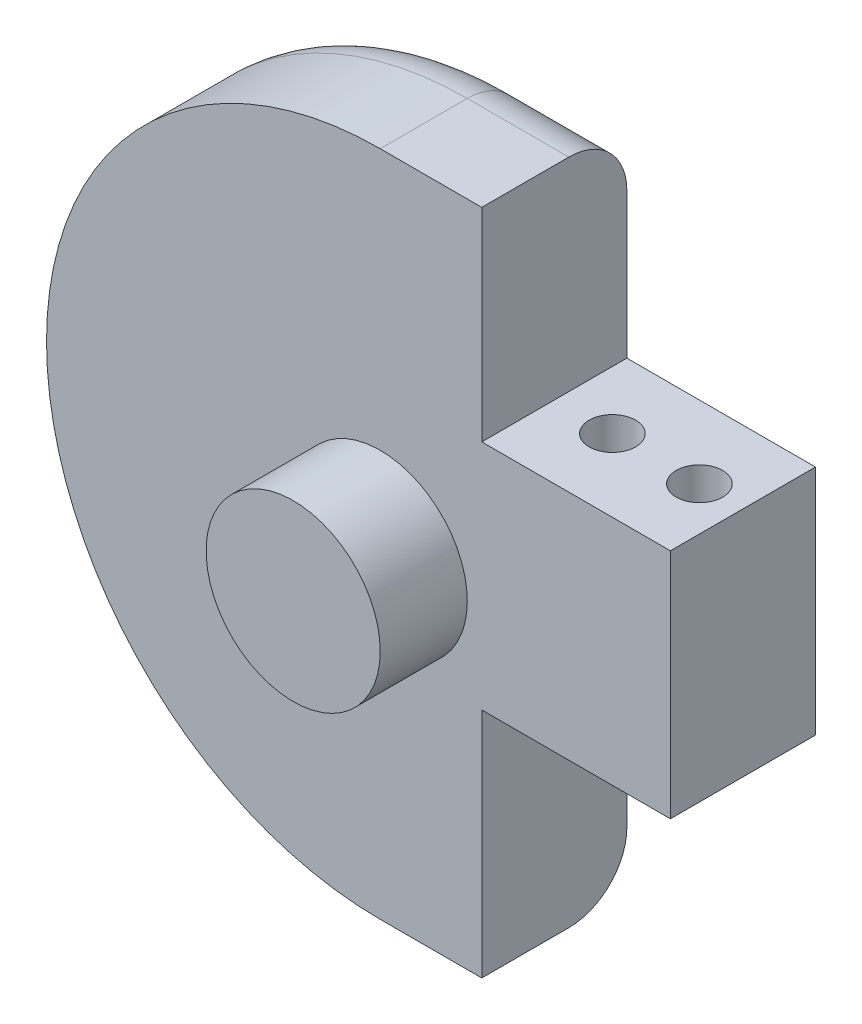
SolidWorks part; units mm, degrees
ref_plane "Front" through (0, 0, 0) normal (0, 0, 1) x (1, 0, 0)
ref_plane "Top" through (0, 0, 0) normal (0, 1, 0) x (1, 0, 0)
ref_plane "Right" through (0, 0, 0) normal (1, 0, 0) x (0, 0, -1)
sketch "Sketch1" plane through (0, 0, 0) normal (0, 0, 1) x (1, 0, 0)
  line L0 (-11, 0) -> (-1, 0) construction
  line L1 (-1, 0) -> (9, 0) construction
  line L2 (3.5, 12) -> (3.5, 5)
  line L3 (3.5, 5) -> (10, 5)
  line L4 (10, -3) -> (3.5, -3)
  line L5 (3.5, -3) -> (3.5, -11)
  line L6 (10, 5) -> (10, -3)
  line L7 (0, 12) -> (3.5, 12)
  line L8 (0, -11) -> (3.5, -11)
  arc A1 (0, 12) -> (0, -11) centre (0, 0.5) ccw
extrude "Boss-Extrude1" add sketch "Sketch1" along normal blind 5
sketch "Sketch2" plane through (0, 0, 0) normal (0, 1, 0) x (1, 0, 0)
  line L0 (10, -2.5) -> (8.5, -2.5) construction
  line L2 (8.5, -2.5) -> (5.5, -2.5) construction
  circle A0 centre (8.5, -2.5) radius 0.8
  circle A1 centre (5.5, -2.5) radius 0.8
extrude "Cut-Extrude1" cut sketch "Sketch2" against normal through all from offset 11
sketch "Sketch4" plane through (0, 0, 0) normal (0, 0, 1) x (1, 0, 0)
  circle A0 centre (0, 0) radius 3
extrude "Boss-Extrude2" add sketch "Sketch4" along normal blind 3 from offset 5
fillet "Fillet1" radius 2 3 edges at (1.75, 12, 0) (1.75, -11, 0) (-11.5, 0.5, 0)
